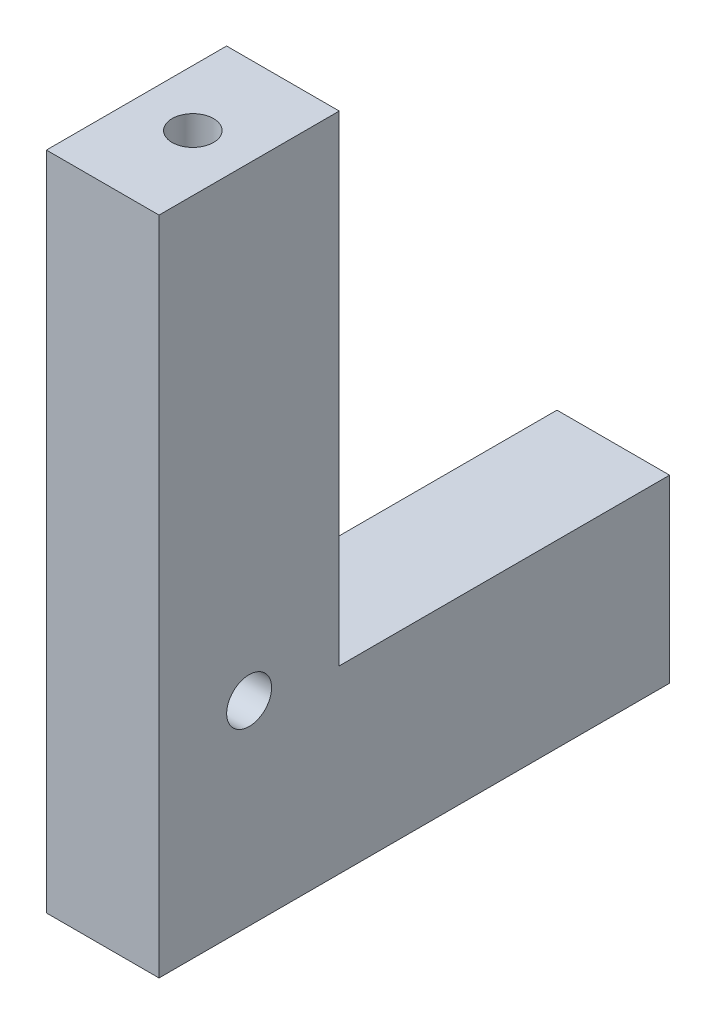
SolidWorks part; units mm, degrees
ref_plane "정면" through (0, 0, 0) normal (0, 0, 1) x (1, 0, 0)
ref_plane "윗면" through (0, 0, 0) normal (0, 1, 0) x (1, 0, 0)
ref_plane "우측면" through (0, 0, 0) normal (1, 0, 0) x (0, 0, -1)
sketch "Sketch1" plane through (0, 0, 0) normal (0, 0, 1) x (1, 0, 0)
  line L1 (0, 0) -> (-9.525, 0)
  line L2 (0, 0) -> (0, 15.24)
  line L3 (0, 15.24) -> (-9.525, 15.24)
  line L4 (-9.525, 0) -> (-9.525, 15.24)
  dimension "D1" = 9.525
  dimension "D2" = 15.24
extrude "Extrude1" add sketch "Sketch1" along normal blind 43.18
sketch "Sketch4" plane through (0, 15.24, 0) normal (0, 1, 0) x (-1, 0, 0)
  line L0 (0, 43.18) -> (0, 0) construction
  line L1 (9.525, 43.18) -> (0, 43.18)
  line L2 (9.525, 43.18) -> (9.525, 27.94)
  line L3 (9.525, 27.94) -> (0, 27.94)
  line L4 (0, 43.18) -> (0, 27.94)
  dimension "D1" = 15.24
extrude "Extrude2" add sketch "Sketch4" along normal blind 40.64
hole_wizard "#6-32 Tapped Hole1" positions "3DSketch3" profile "Sketch7" tap size "#6-32" standard "Ansi Inch"
sketch3d "3DSketch3"
  line L0 (-9.525, 15.24, 0) -> (-9.525, 0, 0) construction
  line L1 (-9.525, 0, 0) -> (0, 0, 0) construction
  point P0 (-4.7625, 11.43, 0)
  point P2 (-4.7625, 3.81, 0)
  point P9 (-19.7665, 16.1139, 0)
  dimension "D1" = 7.62
  dimension "D2" = 4.7625
  dimension "D3" = 4.7625
  dimension "D4" = 3.81
sketch "Sketch7" plane through (-4.7625, 11.43, 0) normal (1, 0, 0) x (0, 1, 0)
  line L0 (0, 0) -> (0, 14.7827)
  line L1 (0, 14.7827) -> (1.3525, 13.97)
  line L2 (1.3525, 13.97) -> (1.3525, 9.906)
  line L3 (1.3525, 9.906) -> (1.7526, 9.906)
  line L4 (1.7526, 9.906) -> (1.7526, 0)
  line L5 (1.7526, 0) -> (0, 0)
  line L10 (0, 14.7827) -> (-1.3526, 13.97) construction
  line L11 (0, -6.35) -> (0, 107.95) construction
  dimension "Tap Drill Dia." = 2.7051
  dimension "Tap Drill Depth" = 13.97
  dimension "Thread Major Dia." = 3.5052
  dimension "Thread Depth" = 9.906
  dimension "Drill Angle" = 118
hole_wizard "#6 Clearance Hole1" positions "3DSketch4" profile "Sketch8" hole size "#6" standard "Ansi Inch"
sketch3d "3DSketch4"
  line L1 (0, 55.88, 27.94) -> (0, 15.24, 27.94) construction
  line L3 (0, 0, 43.18) -> (0, 0, 0) construction
  point P0 (0, 16.51, 35.56)
  dimension "D1" = 16.51
  dimension "D2" = 7.62
sketch "Sketch8" plane through (0, 16.51, 35.56) normal (0, 1, 0) x (0, 0, -1)
  line L0 (0, 0) -> (0, 11.0468)
  line L1 (0, 11.0468) -> (1.8986, 9.906)
  line L2 (1.8986, 9.906) -> (1.8986, 0)
  line L5 (1.8986, 0) -> (0, 0)
  line L10 (0, 11.0468) -> (-1.8987, 9.906) construction
  line L11 (0, -6.35) -> (0, 107.95) construction
  dimension "Hole Dia." = 3.7973
  dimension "Hole Depth" = 9.906
  dimension "Drill Angle" = 118
hole_wizard "#6-32 Tapped Hole2" positions "3DSketch5" profile "Sketch9" tap size "#6-32" standard "Ansi Inch"
sketch3d "3DSketch5"
  line L0 (0, 55.88, 43.18) -> (0, 55.88, 27.94) construction
  line L1 (-9.525, 55.88, 43.18) -> (0, 55.88, 43.18) construction
  point P0 (-4.7625, 55.88, 35.56)
  dimension "D1" = 4.7625
  dimension "D2" = 7.62
sketch "Sketch9" plane through (-4.7625, 55.88, 35.56) normal (1, 0, 0) x (0, 0, 1)
  line L0 (0, 0) -> (0, 14.7827)
  line L1 (0, 14.7827) -> (1.3525, 13.97)
  line L2 (1.3525, 13.97) -> (1.3525, 9.906)
  line L3 (1.3525, 9.906) -> (1.7526, 9.906)
  line L4 (1.7526, 9.906) -> (1.7526, 0)
  line L5 (1.7526, 0) -> (0, 0)
  line L10 (0, 14.7827) -> (-1.3526, 13.97) construction
  line L11 (0, -6.35) -> (0, 107.95) construction
  dimension "Tap Drill Dia." = 2.7051
  dimension "Tap Drill Depth" = 13.97
  dimension "Thread Major Dia." = 3.5052
  dimension "Thread Depth" = 9.906
  dimension "Drill Angle" = 118
